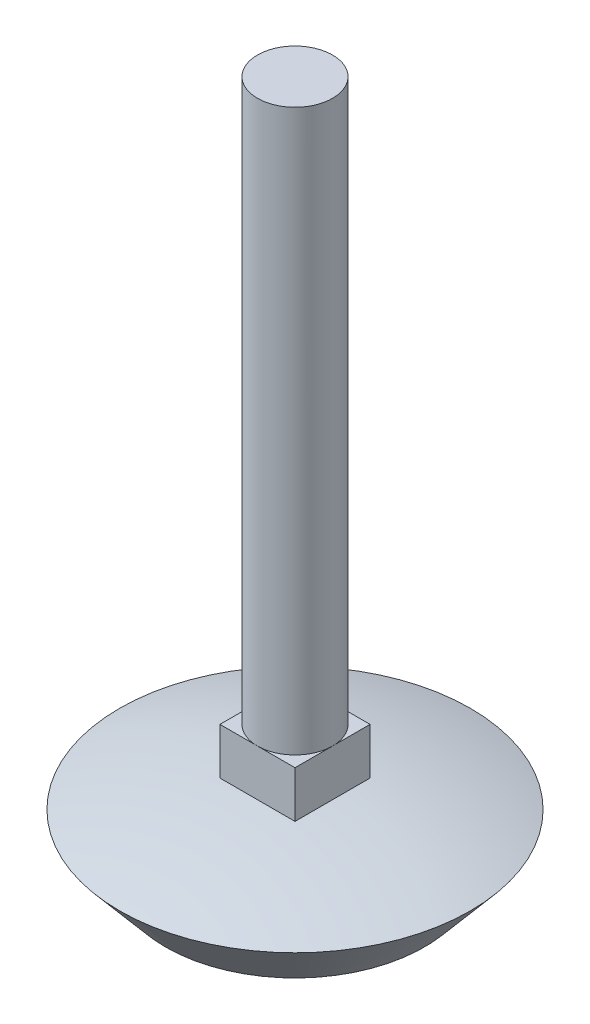
SolidWorks part; units mm, degrees
ref_plane "Front Plane" through (0, 0, 0) normal (0, 0, 1) x (1, 0, 0)
ref_plane "Top Plane" through (0, 0, 0) normal (0, 1, 0) x (1, 0, 0)
ref_plane "Right Plane" through (0, 0, 0) normal (1, 0, 0) x (0, 0, -1)
sketch "Sketch1" plane through (0, 0, 0) normal (0, 0, 1) x (1, 0, 0)
  line L0 (168.529, 853.44) -> (174.244, 860.2028) construction
  line L1 (130.556, 860.2028) -> (136.271, 853.44) construction
  line L2 (136.271, 853.44) -> (168.529, 853.44) construction
  line L3 (130.556, 860.2028) -> (174.244, 860.2028) construction
  line L4 (152.4, 863.6) -> (152.4, 853.44) construction
  line L5 (152.4, 863.6) -> (152.4, 860.044) construction
  line L6 (147.7264, 869.3912) -> (147.7264, 939.2412) construction
  line L7 (157.0736, 869.3912) -> (147.7264, 869.3912) construction
  line L8 (157.0736, 939.2412) -> (157.0736, 869.3912) construction
  line L9 (147.7264, 939.2412) -> (157.0736, 939.2412) construction
  line L10 (147.7264, 869.3912) -> (157.0736, 869.3912) construction
  line L11 (147.7264, 863.6) -> (147.7264, 869.3912) construction
  line L12 (157.0736, 863.6) -> (157.0736, 869.3912) construction
  line L13 (147.7264, 863.6) -> (157.0736, 863.6) construction
  line L14 (152.4, 939.2412) -> (152.4, 853.44)
  line L15 (152.4, 853.44) -> (136.271, 853.44)
  line L16 (136.271, 853.44) -> (130.556, 860.2028)
  line L17 (152.4, 939.2412) -> (147.7264, 939.2412)
  line L18 (147.7264, 939.2412) -> (147.7264, 863.6)
  arc A0 (174.244, 860.2028) -> (130.556, 860.2028) centre (152.4, 794.8885) ccw construction
  arc A1 (147.7264, 863.6) -> (130.556, 860.2028) centre (152.4, 794.8885) ccw
revolve "Revolve1" add sketch "Sketch1" angle 360 about L14
sketch "Sketch2" plane through (0, 0, 0) normal (0, 0, 1) x (1, 0, 0)
  line L0 (157.0736, 863.6) -> (157.0736, 869.3912)
  line L1 (157.0736, 863.6) -> (157.0736, 939.2412) construction
  line L2 (157.0736, 869.3912) -> (147.7264, 869.3912)
  line L3 (147.7264, 939.2412) -> (147.7264, 863.6) construction
  line L4 (147.7264, 869.3912) -> (147.7264, 863.6)
  line L5 (147.7264, 863.6) -> (157.0736, 863.6)
extrude "Extrude1" add sketch "Sketch2" along normal mid plane 9.3472
